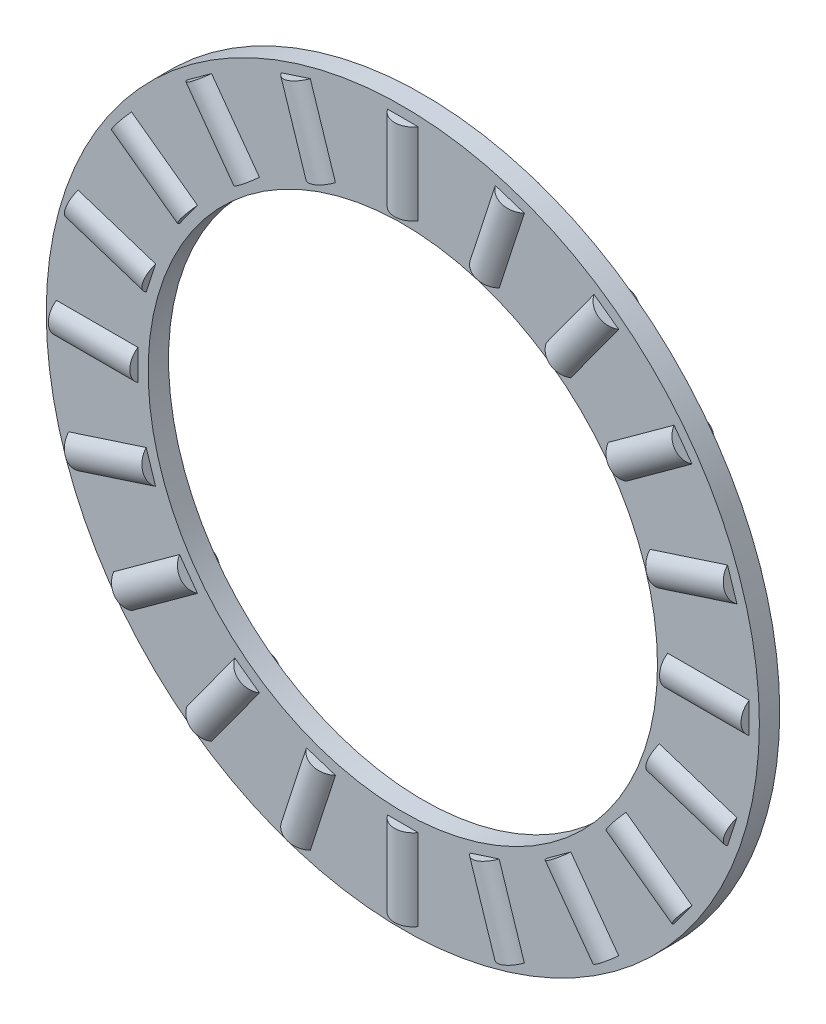
SolidWorks part; units mm, degrees
ref_plane "Plan de face" through (0, 0, 0) normal (0, 0, 1) x (1, 0, 0)
ref_plane "Plan de dessus" through (0, 0, 0) normal (0, 1, 0) x (1, 0, 0)
ref_plane "Plan de droite" through (0, 0, 0) normal (1, 0, 0) x (0, 0, -1)
sketch "Esquisse1" plane through (0, 0, 0) normal (0, 0, 1) x (1, 0, 0)
  circle A0 centre (0, 0) radius 35
  circle A1 centre (0, 0) radius 25
  dimension "D1" = 50
  dimension "D2" = 70
extrude "Boss.-Extru.1" add sketch "Esquisse1" along normal blind 2
sketch "Esquisse2" plane through (0, 0, 0) normal (0, 1, 0) x (1, 0, 0)
  line L0 (0, 0) -> (0, -2) construction
  line L1 (-25, -2) -> (25, -2) construction
  circle A0 centre (0, -1) radius 1.8
  dimension "D1" = 3.6
extrude "Boss.-Extru.2" add sketch "Esquisse2" along normal blind 8 from offset 26
pattern_circular "Répétition circulaire1" count 20 over 360 about axis through (0, 0, 0) along (0, 0, 1) of "Boss.-Extru.2"
